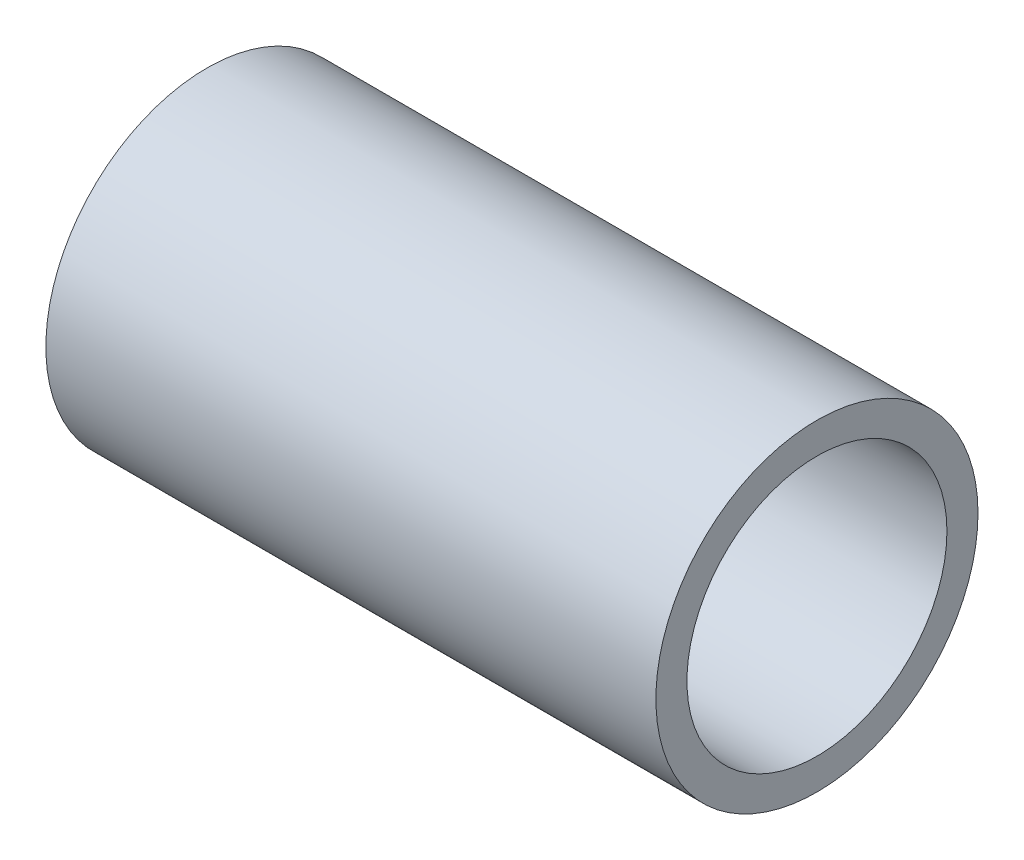
SolidWorks part; units mm, degrees
material "PET"
ref_plane "Front Plane" through (0, 0, 0) normal (0, 0, 1) x (1, 0, 0)
ref_plane "Top Plane" through (0, 0, 0) normal (0, 1, 0) x (1, 0, 0)
ref_plane "Right Plane" through (0, 0, 0) normal (1, 0, 0) x (0, 0, -1)
sketch "Sketch1" plane through (0, 0, 0) normal (1, 0, 0) x (0, 0, -1)
  circle A0 centre (0, 0) radius 8.382
  circle A1 centre (0, 0) radius 6.7659
  dimension "D1" = 16.764
  dimension "D2" = 13.5318
extrude "Boss-Extrude1" add sketch "Sketch1" along normal blind 31.75
